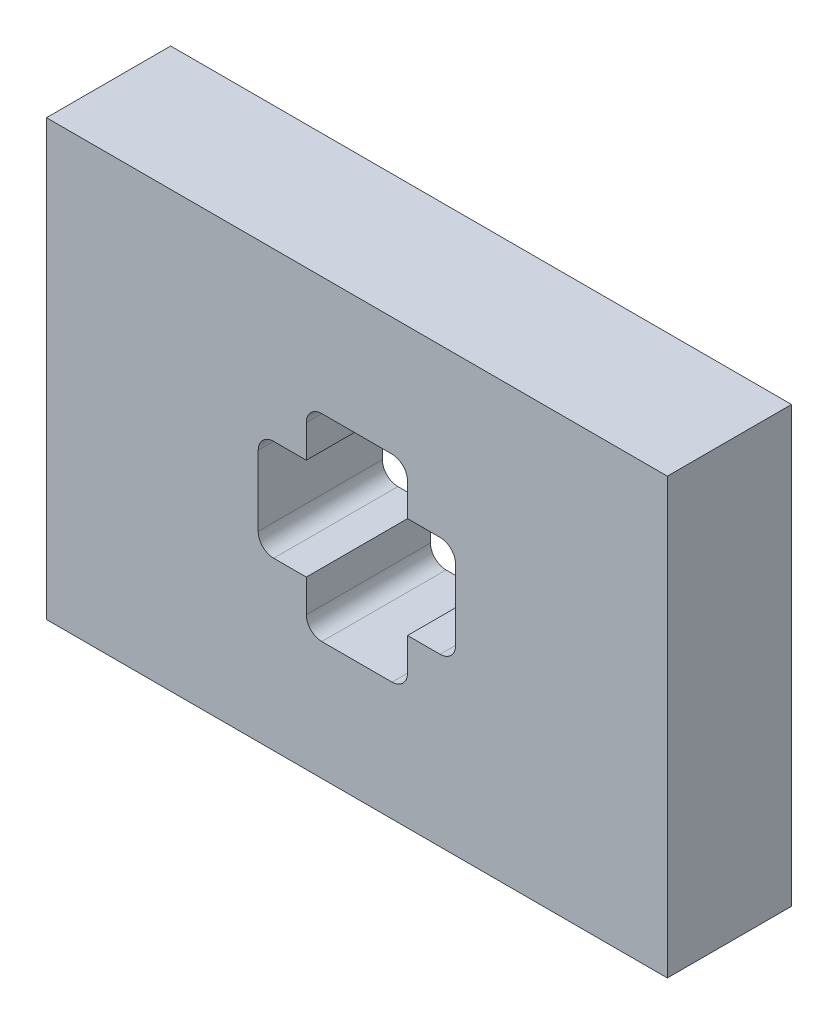
SolidWorks part; units mm, degrees
ref_plane "Front Plane" through (0, 0, 0) normal (0, 0, 1) x (1, 0, 0)
ref_plane "Top Plane" through (0, 0, 0) normal (0, 1, 0) x (1, 0, 0)
ref_plane "Right Plane" through (0, 0, 0) normal (1, 0, 0) x (0, 0, -1)
sketch "Sketch1" plane through (0, 0, 0) normal (0, 0, 1) x (1, 0, 0)
  line L0 (0, 0) -> (0, 18506.4536) construction
  line L1 (0, 0) -> (-18506.4536, 0) construction
  line L2 (-8.15, 13.4) -> (-8.15, 8.15)
  line L3 (5.65, -15.9) -> (-5.65, -15.9)
  line L4 (15.9, -5.65) -> (15.9, 5.65)
  line L5 (5.65, 15.9) -> (-5.65, 15.9)
  line L6 (-15.9, -5.65) -> (-15.9, 5.65)
  line L7 (8.15, -8.15) -> (-8.15, 8.15) construction
  line L8 (8.15, 8.15) -> (-8.15, -8.15) construction
  line L9 (-13.4, -8.15) -> (-8.15, -8.15)
  line L10 (8.15, 13.4) -> (8.15, 8.15)
  line L11 (-13.4, 8.15) -> (-8.15, 8.15)
  line L12 (-8.15, -8.15) -> (-8.15, -13.4)
  line L13 (8.15, -8.15) -> (13.4, -8.15)
  line L14 (8.15, -8.15) -> (8.15, -13.4)
  line L15 (8.15, 8.15) -> (13.4, 8.15)
  line L17 (50, -35) -> (-50, -35)
  line L18 (50, -35) -> (50, 35)
  line L19 (50, 35) -> (-50, 35)
  line L20 (-50, -35) -> (-50, 35)
  line L21 (50, -35) -> (-50, 35) construction
  line L22 (50, 35) -> (-50, -35) construction
  arc A0 (-8.15, 13.4) -> (-5.65, 15.9) centre (-5.65, 13.4) cw
  arc A1 (-13.4, 8.15) -> (-15.9, 5.65) centre (-13.4, 5.65) ccw
  arc A2 (-13.4, -8.15) -> (-15.9, -5.65) centre (-13.4, -5.65) cw
  arc A3 (-5.65, -15.9) -> (-8.15, -13.4) centre (-5.65, -13.4) cw
  arc A4 (5.65, -15.9) -> (8.15, -13.4) centre (5.65, -13.4) ccw
  arc A5 (15.9, -5.65) -> (13.4, -8.15) centre (13.4, -5.65) cw
  arc A6 (15.9, 5.65) -> (13.4, 8.15) centre (13.4, 5.65) ccw
  arc A7 (8.15, 13.4) -> (5.65, 15.9) centre (5.65, 13.4) ccw
  point P5 (0, 0)
  point P8 (-8.15, 15.9)
  point P23 (-15.9, 8.15)
  point P26 (-15.9, -8.15)
  point P29 (-8.15, -15.9)
  point P32 (8.15, -15.9)
  point P35 (15.9, -8.15)
  point P38 (15.9, 8.15)
  point P41 (8.15, 15.9)
  point P42 (0, 0)
  dimension "D7" = 2.5
  dimension "D8" = 2.5
  dimension "D1" = 31.8
  dimension "D2" = 31.8
  dimension "D3" = 8.15
  dimension "D4" = 8.15
  dimension "D5" = 15.9
  dimension "D6" = 15.9
  dimension "D9" = 100
  dimension "D10" = 70
extrude "Boss-Extrude1" add sketch "Sketch1" along normal blind 20
